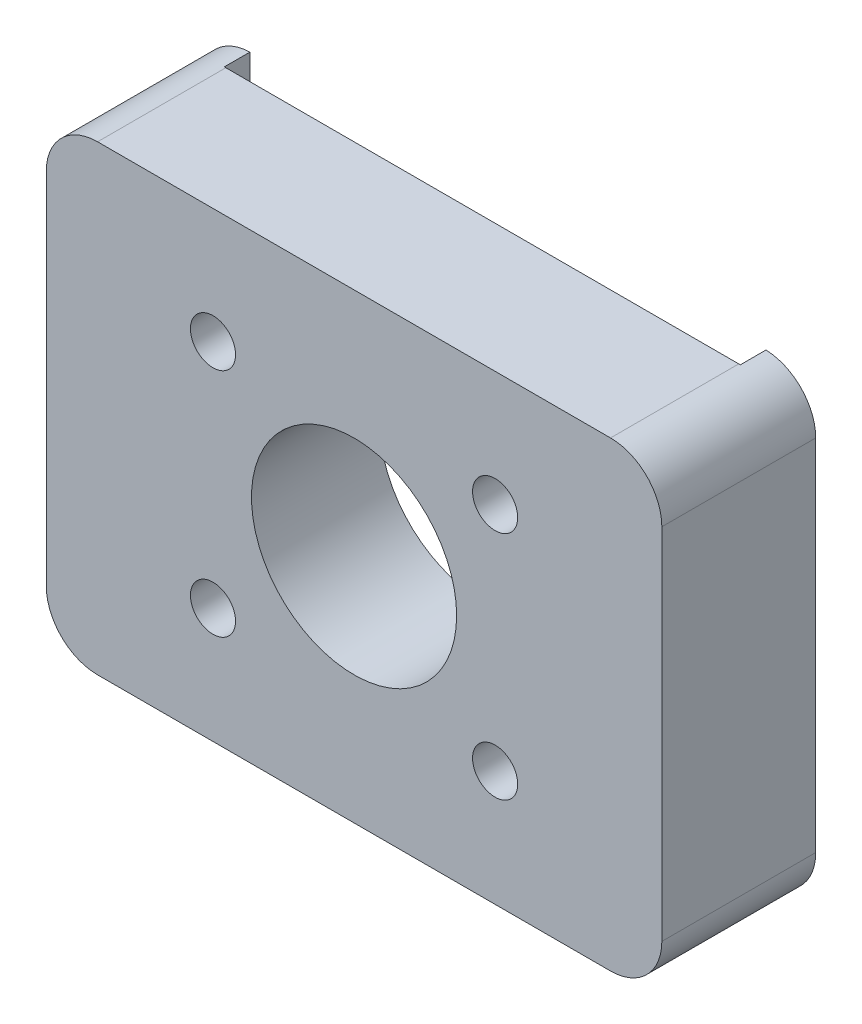
SolidWorks part; units mm, degrees
ref_plane "Front Plane" through (0, 0, 0) normal (0, 0, 1) x (1, 0, 0)
ref_plane "Top Plane" through (0, 0, 0) normal (0, 1, 0) x (1, 0, 0)
ref_plane "Right Plane" through (0, 0, 0) normal (1, 0, 0) x (0, 0, -1)
sketch "Sketch1" plane through (0, 0, 0) normal (0, 0, 1) x (1, 0, 0)
  line L0 (-27.5, 45) -> (-27.5, -45) construction
  line L1 (-50, 45) -> (50, 45)
  line L2 (-60, 35) -> (-60, -35)
  line L3 (-50, -45) -> (50, -45)
  line L4 (60, 35) -> (60, -35)
  line L5 (-60, 45) -> (60, -45) construction
  line L6 (-60, -45) -> (60, 45) construction
  line L7 (27.5, 45) -> (27.5, -45) construction
  line L8 (-60, 22.5) -> (60, 22.5) construction
  line L9 (-60, -22.5) -> (60, -22.5) construction
  arc A0 (-60, -35) -> (-50, -45) centre (-50, -35) ccw
  arc A1 (50, -45) -> (60, -35) centre (50, -35) ccw
  arc A2 (60, 35) -> (50, 45) centre (50, 35) ccw
  arc A3 (-50, 45) -> (-60, 35) centre (-50, 35) ccw
  circle A4 centre (-27.5, 22.5) radius 4.4
  circle A5 centre (27.5, 22.5) radius 4.4
  circle A6 centre (-27.5, -22.5) radius 4.4
  circle A7 centre (27.5, -22.5) radius 4.4
  circle A8 centre (0, 0) radius 20
  point P0 (0, 0)
  dimension "D3" = 10
  dimension "D1" = 120
  dimension "D2" = 90
  dimension "D4" = 22.5
  dimension "D5" = 22.5
  dimension "D6" = 32.5
  dimension "D7" = 32.5
extrude "Boss-Extrude1" add sketch "Sketch1" along normal blind 25
sketch "Sketch2" plane through (0, 0, 0) normal (0, 0, -1) x (-1, 0, 0)
  line L0 (-50.3, 44.9955) -> (-50.3, -44.9955)
  line L2 (-60, -35) -> (-60, 35)
  line L4 (60, -35) -> (60, 35)
  line L5 (-60, -45) -> (60, 45) construction
  line L6 (-60, 45) -> (60, -45) construction
  line L7 (50.3, 44.9955) -> (50.3, -44.9955)
  arc A0 (-50.3, -44.9955) -> (-60, -35) centre (-50, -35) cw
  arc A1 (50.3, -44.9955) -> (60, -35) centre (50, -35) ccw
  arc A2 (60, 35) -> (50.3, 44.9955) centre (50, 35) ccw
  arc A3 (-50.3, 44.9955) -> (-60, 35) centre (-50, 35) ccw
  point P0 (0, 0)
  dimension "D3" = 10
  dimension "D1" = 120
  dimension "D2" = 90
  dimension "D4" = 9.7
  dimension "D5" = 9.7
extrude "Boss-Extrude2" add sketch "Sketch2" along normal blind 5
